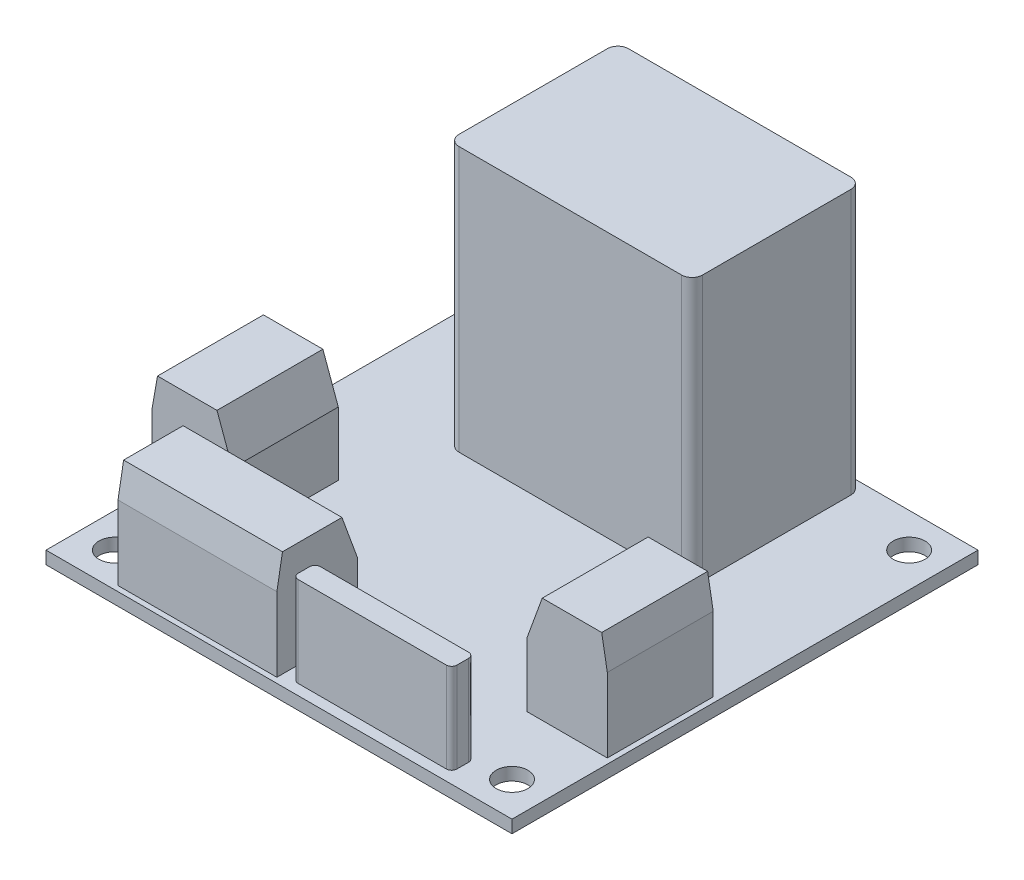
SolidWorks part; units mm, degrees
ref_plane "Front Plane" through (0, 0, 0) normal (0, 0, 1) x (1, 0, 0)
ref_plane "Top Plane" through (0, 0, 0) normal (0, 1, 0) x (1, 0, 0)
ref_plane "Right Plane" through (0, 0, 0) normal (1, 0, 0) x (0, 0, -1)
sketch "Sketch1" plane through (0, 0, 0) normal (0, 1, 0) x (1, 0, 0)
  line L1 (-22, 22) -> (22, 22)
  line L2 (-22, 22) -> (-22, -22)
  line L3 (-22, -22) -> (22, -22)
  line L4 (22, 22) -> (22, -22)
  line L5 (-22, 22) -> (22, -22) construction
  line L6 (-22, -22) -> (22, 22) construction
  point P0 (0, 0)
  dimension "D1" = 44
  dimension "D2" = 44
extrude "Boss-Extrude1" add sketch "Sketch1" along normal blind 1.2
sketch "Sketch2" plane through (0, 1.2, 0) normal (0, 1, 0) x (1, 0, 0)
  line L1 (-11.5, 21.5) -> (11.5, 21.5)
  line L2 (-11.5, 21.5) -> (-11.5, 5.5)
  line L3 (-11.5, 5.5) -> (11.5, 5.5)
  line L4 (11.5, 21.5) -> (11.5, 5.5)
  line L5 (22, 22) -> (-22, 22) construction
  point P6 (0, 5.5)
  dimension "D1" = 23
  dimension "D2" = 16
  dimension "D3" = 0.5
extrude "Boss-Extrude2" add sketch "Sketch2" along normal blind 25
sketch "Sketch3" plane through (0, 1.2, 0) normal (0, 1, 0) x (1, 0, 0)
  line L1 (-21.5, -2.5) -> (-13.9, -2.5)
  line L2 (-21.5, -2.5) -> (-21.5, -12.5)
  line L3 (-21.5, -12.5) -> (-13.9, -12.5)
  line L4 (-13.9, -2.5) -> (-13.9, -12.5)
  line L5 (-22, -22) -> (22, -22) construction
  line L6 (-22, 22) -> (-22, -22) construction
  dimension "D1" = 7.6
  dimension "D2" = 10
  dimension "D3" = 9.5
  dimension "D4" = 0.5
extrude "Boss-Extrude3" add sketch "Sketch3" along normal blind 10
mirror "Mirror1" about plane through (0, 0, 0) normal (1, 0, 0) of "Boss-Extrude3"
fillet "Fillet1" radius 1 4 edges at (11.5, 13.7, -5.5) (11.5, 13.7, -21.5) (-11.5, 13.7, -21.5) (-11.5, 13.7, -5.5)
sketch "Sketch4" plane through (0, 1.2, 0) normal (0, 1, 0) x (1, 0, 0)
  line L0 (-22, -22) -> (22, -22) construction
  line L1 (-15.7, -21.5) -> (-0.7, -21.5)
  line L2 (-15.7, -21.5) -> (-15.7, -13.9)
  line L3 (-15.7, -13.9) -> (-0.7, -13.9)
  line L4 (-0.7, -21.5) -> (-0.7, -13.9)
  line L5 (-22, 22) -> (-22, -22) construction
  dimension "D1" = 7.6
  dimension "D2" = 15
  dimension "D3" = 0.5
  dimension "D4" = 6.3
extrude "Boss-Extrude4" add sketch "Sketch4" along normal blind 10
chamfer "Chamfer2" distance 3 angle 10 3 edges at (21.5, 11.2, 7.5) (-21.5, 11.2, 7.5) (-8.2, 11.2, 21.5)
chamfer "Chamfer1" distance 4 angle 20 3 edges at (13.9, 11.2, 7.5) (-13.9, 11.2, 7.5) (-8.2, 11.2, 13.9)
sketch "Sketch5" plane through (0, 1.2, 0) normal (0, 1, 0) x (1, 0, 0)
  line L0 (-0.7, -21.5) -> (-0.7, -13.9) construction
  line L1 (0.3, -18.9) -> (15.3, -18.9)
  line L2 (0.3, -18.9) -> (0.3, -21)
  line L3 (0.3, -21) -> (15.3, -21)
  line L4 (15.3, -18.9) -> (15.3, -21)
  line L5 (-22, -22) -> (22, -22) construction
  dimension "D1" = 15
  dimension "D2" = 2.1
  dimension "D3" = 1
  dimension "D4" = 1
extrude "Boss-Extrude5" add sketch "Sketch5" along normal blind 8.5
fillet "Fillet2" radius 0.5 4 edges at (15.3, 5.45, 18.9) (0.3, 5.45, 18.9) (0.3, 5.45, 21) (15.3, 5.45, 21)
sketch "Sketch6" plane through (0, 1.2, 0) normal (0, 1, 0) x (1, 0, 0)
  circle A0 centre (-18.75, 18.75) radius 1.5
  circle A1 centre (18.75, 18.75) radius 1.5
  circle A2 centre (18.75, -18.75) radius 1.5
  circle A3 centre (-18.75, -18.75) radius 1.5
  dimension "D1" = 3
  dimension "D2" = 37.5
  dimension "D3" = 37.5
  dimension "D4" = 18.75
  dimension "D5" = 18.75
extrude "Cut-Extrude1" cut sketch "Sketch6" against normal through all
equation "\"D4@Sketch6\"=37.5/2"
equation "\"D5@Sketch6\"=37.5/2"
